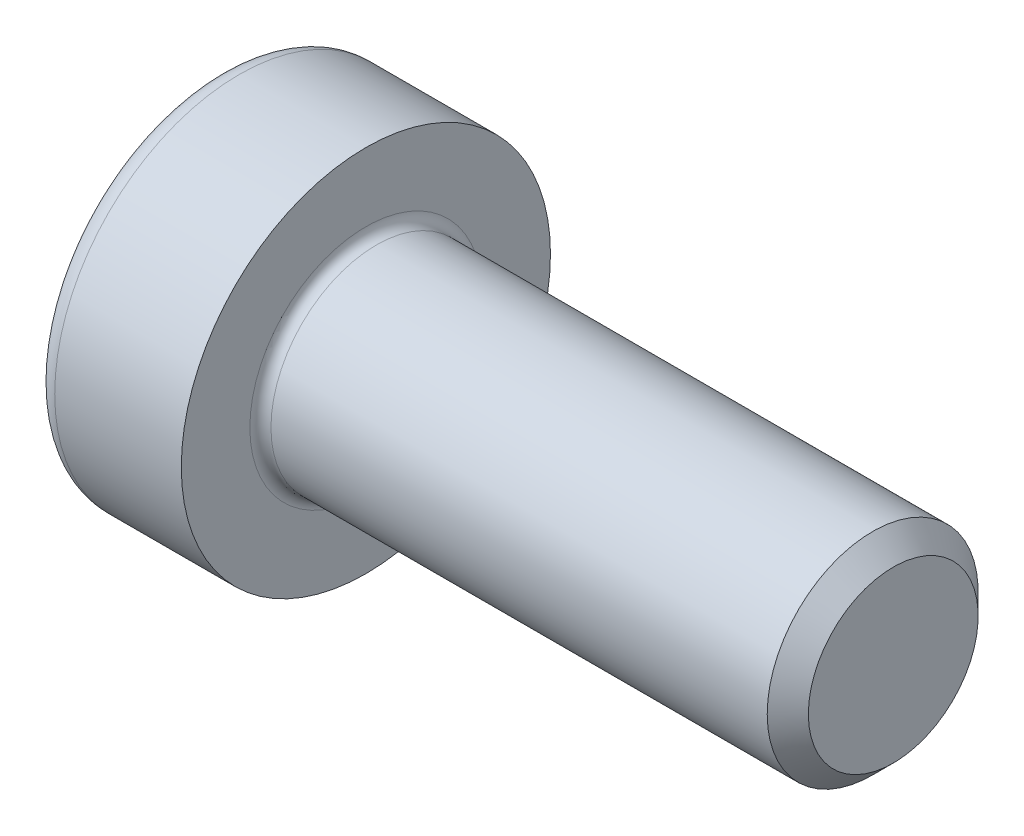
SolidWorks part; units mm, degrees
revolve "Base-Revolve" add sketch "BodySke"
sketch "BodySke" plane through (0, 0, 0) normal (0, 0, 1) x (1, 0, 0)
  line L0 (0, 0) -> (0, 3.5)
  line L1 (0, 3.5) -> (2.8, 3.5)
  line L2 (2.8, 3.5) -> (2.8, 2)
  line L3 (2.8, 2) -> (12.41, 2)
  line L4 (12.8, 1.61) -> (12.8, 0)
  line L5 (12.8, 0) -> (0, 0)
  line L6 (-31.75, 0) -> (127, 0) construction
  line L8 (12.8, 1.61) -> (12.41, 2)
  line L10 (12.8, -1.61) -> (12.41, -2) construction
  line L11 (3.5, 4.525) -> (3.5, -1.825) construction
  line L12 (6.3, 4.525) -> (6.3, -1.825) construction
  line L13 (-47.2, 4.525) -> (-47.2, -1.825) construction
  dimension "Head_ht" = 2.8
  dimension "Length" = 10
  dimension "Body_ch_ang" = 45
  dimension "Diameter" = 4
  dimension "Minor_dia" = 3.22
  dimension "Advance" = 0.7
  dimension "Thread_nom" = 6.5
  dimension "Thread_length" = 60
  dimension "Head_dia" = 7
cosmetic thread "ThreadCosmetic" [suppressed]
fillet "Fillet1" radius 0.2 1 edges at (2.8, 0, 2)
fillet "Fillet2" radius 0.4 1 edges at (0, 0, 3.5)
ref_plane "Plane1" through (0, 0, 0) normal (0, 0, 1) x (1, 0, 0)
ref_plane "Plane2" through (0, 0, 0) normal (0, 1, 0) x (1, 0, 0)
ref_plane "Plane3" through (0, 0, 0) normal (1, 0, 0) x (0, 0, -1)
sketch "HexSke" plane through (0, 0, 0) normal (-1, 0, 0) x (0, 0.5, 0.866)
  line L0 (0.866, 1.5) -> (-0.866, 1.5)
  line L1 (-0.866, 1.5) -> (-1.7321, 0)
  line L2 (0.866, 1.5) -> (1.7321, 0)
  line L3 (0.866, -1.5) -> (1.7321, 0)
  line L4 (0.866, -1.5) -> (-0.866, -1.5)
  line L5 (-0.866, -1.5) -> (-1.7321, 0)
  dimension "D1" = 1.5
  dimension "D2" = 1.5
  dimension "Hex_size" = 3
extrude "Hex" cut sketch "HexSke" against normal blind 1.6
sketch "PilotSke" plane through (0, 0, 0) normal (0, 0, 1) x (1, 0, 0)
  line L0 (0, 1.5) -> (1.6, 1.5)
  line L1 (1.6, 1.5) -> (1.8887, 1)
  line L2 (-31.75, 0) -> (127, 0) construction
  line L3 (3.8774, 0) -> (0, 0)
  line L4 (0, 0) -> (0, 1.5)
  line L5 (1.8887, 1) -> (3.3, 1)
  line L6 (0, 0) -> (47.625, 0) construction
  line L7 (3.3, 1) -> (3.8774, 0)
  dimension "D1" = 1.5
  dimension "D2" = 60
  dimension "Depth" = 1.6
  dimension "Pilot_dia" = 2
  dimension "Pilot_Depth" = 3.3
revolve "Hex-PreBroach" cut sketch "PilotSke" angle 360 about L6
sketch "ThdSchSke" plane through (0, 0, 0) normal (0, 0, 1) x (1, 0, 0)
  line L0 (6.3, -1.61) -> (6.0269, -2)
  line L1 (6.3, -1.61) -> (6.5731, -2)
  line L2 (6.5731, -2) -> (6.5731, -2.5)
  line L3 (-3.175, 0) -> (5.1513, 0) construction
  line L4 (0, 3.1) -> (0, -3.1) construction
  line L5 (6.5731, -2.5) -> (6.0269, -2.5)
  line L6 (6.0269, -2.5) -> (6.0269, -2)
  dimension "Thread_minor" = 3.22
  dimension "Diameter" = 4
  dimension "Start" = 6.3
revolve "ThreadSchematic" [suppressed] cut sketch "ThdSchSke" angle 360 about L3
pattern_linear "ThdSchPat" [suppressed]
equation "\"D2@HexSke\" = \"Hex_size@HexSke\" / 2"
equation "\"D1@HexSke\" = \"Hex_size@HexSke\" / 2"
equation "\"D1@PilotSke\" = \"Hex_size@HexSke\" / 2"
equation "\"Thread_minor@ThreadCosmetic\"  =  \"Minor_dia@BodySke\""
equation "\"Depth@PilotSke\" =  \"Key_eng@Hex\""
equation "\"Thread_length@ThreadCosmetic\" = ((sgn( (\"Length@BodySke\" - \"Advance@BodySke\" * 3.0) - \"Thread_nom@BodySke\" )-1)*( (\"Length@BodySke\" - \"Advance@BodySke\" * 3.0) - \"Thread_nom@BodySke\" ))/-2+ \"Thread_nom@BodySke\""
equation "\"Thread_minor@ThdSchSke\" = \"Minor_dia@BodySke\""
equation "\"Diameter@ThdSchSke\" = \"Diameter@BodySke\""
equation "\"Overcut@ThdSchSke\" = \"Diameter@BodySke\" * 1.25"
equation "\"Start@ThdSchSke\" = \"Head_ht@BodySke\" + \"Length@BodySke\" - \"Thread_length@ThreadCosmetic\"  '---Non-countersunk---"
equation "\"Num_threads@ThdSchPat\" = int( \"Thread_length@ThreadCosmetic\" / \"Advance@BodySke\" + 0.999 )  + 1"
equation "\"Advance@ThdSchPat\" = \"Thread_length@ThreadCosmetic\" /  (\"Num_threads@ThdSchPat\" - 1) 'relax it"
equation "\"Num_threads@ThdSchPat\" = \"Num_threads@ThdSchPat\" - sgn( \"Num_threads@ThdSchPat\" - 1) '---chamfered tips only---"
